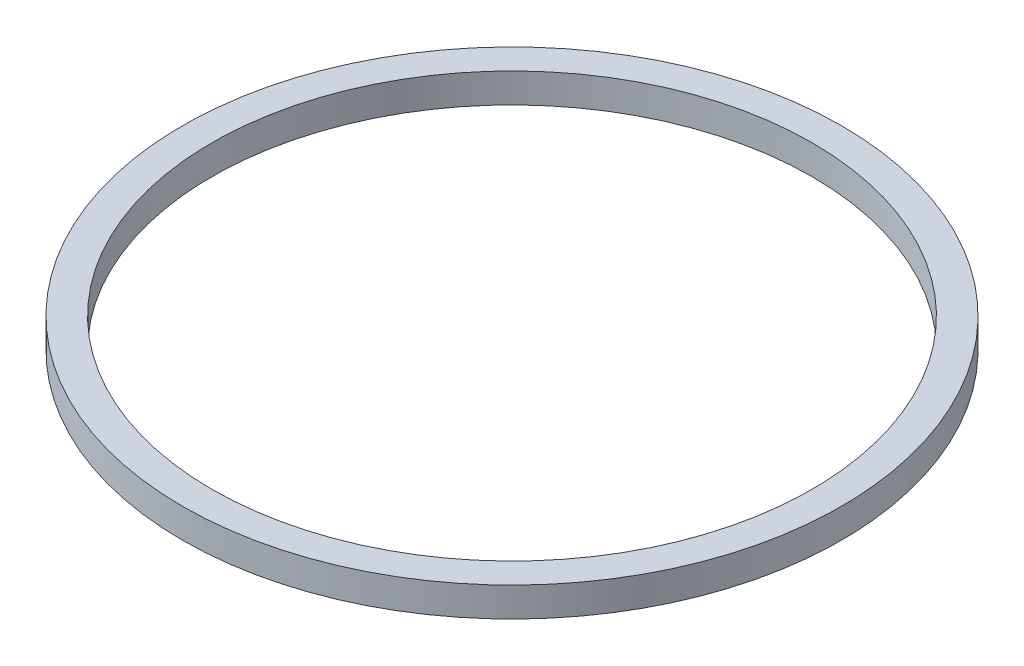
SolidWorks part; units mm, degrees
ref_plane "前视基准面" through (0, 0, 0) normal (0, 0, 1) x (1, 0, 0)
ref_plane "上视基准面" through (0, 0, 0) normal (0, 1, 0) x (1, 0, 0)
ref_plane "右视基准面" through (0, 0, 0) normal (1, 0, 0) x (0, 0, -1)
sketch "草图1" plane through (0, 0, 0) normal (0, 0, 1) x (1, 0, 0)
  line L0 (0, 77.1441) -> (0, -87.8701) construction
  line L1 (-61.6053, 0) -> (62.4304, 0) construction
  line L2 (25.5, 0) -> (25.5, 2.5)
  line L3 (28, 0) -> (28, 2.5)
  line L4 (25.5, 2.5) -> (28, 2.5)
  line L5 (25.5, 0) -> (28, 0)
  dimension "D1" = 25.5
  dimension "D2" = 28
  dimension "D3" = 2.5
revolve "旋转1" add sketch "草图1" angle 360 about L0
cosmetic thread "装饰螺纹线1" parameters "D1"=2.5, "D2"=52
